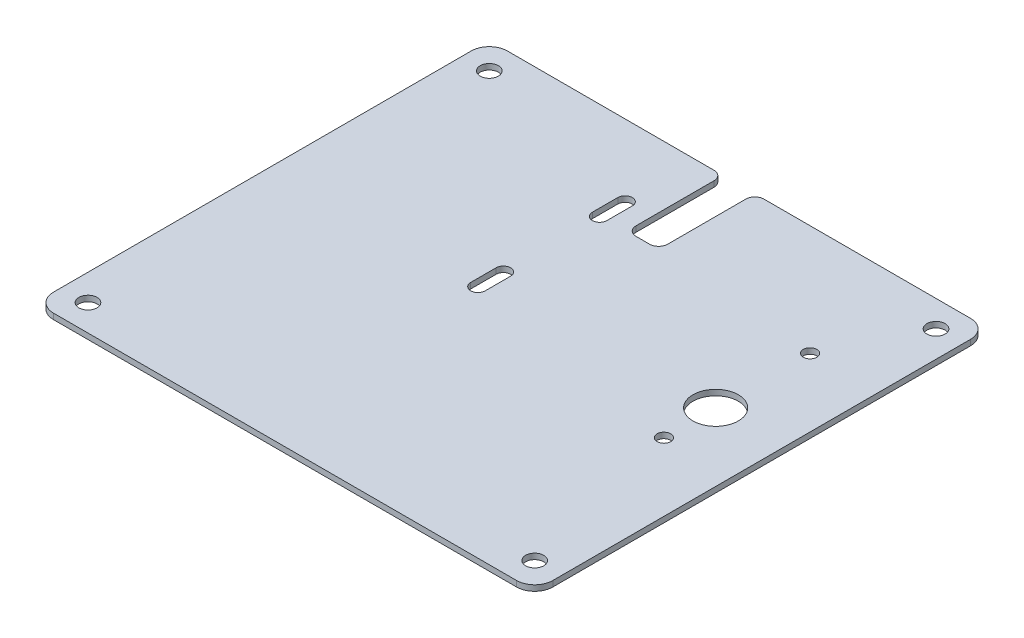
SolidWorks part; units mm, degrees
ref_plane "Front Plane" through (0, 0, 0) normal (0, 0, 1) x (1, 0, 0)
ref_plane "Top Plane" through (0, 0, 0) normal (0, 1, 0) x (1, 0, 0)
ref_plane "Right Plane" through (0, 0, 0) normal (1, 0, 0) x (0, 0, -1)
sketch "Sketch1" plane through (0, 0, 0) normal (0, 1, 0) x (1, 0, 0)
  line L0 (0, 50.038) -> (0, 69.85) construction
  line L1 (69.85, 63.5) -> (4.445, 63.5)
  line L2 (69.85, 63.5) -> (69.85, -63.5)
  line L3 (69.85, -63.5) -> (-69.85, -63.5)
  line L4 (-69.85, 63.5) -> (-69.85, -63.5)
  line L5 (69.85, 63.5) -> (-69.85, -63.5) construction
  line L6 (69.85, -63.5) -> (-69.85, 63.5) construction
  line L7 (-4.445, 63.5) -> (-69.85, 63.5)
  line L8 (4.445, 36.576) -> (-4.445, 36.576)
  line L9 (4.445, 36.576) -> (4.445, 63.5)
  line L11 (-4.445, 36.576) -> (-4.445, 63.5)
  line L12 (4.445, 36.576) -> (-4.445, 63.5) construction
  line L13 (4.445, 63.5) -> (-4.445, 36.576) construction
  line L14 (-11.811, 43.434) -> (-11.811, 36.322) construction
  line L15 (-9.779, 43.434) -> (-9.779, 36.322)
  line L16 (-13.843, 43.434) -> (-13.843, 36.322)
  line L17 (-11.811, 9.398) -> (-11.811, 2.286) construction
  line L18 (-9.779, 9.398) -> (-9.779, 2.286)
  line L19 (-13.843, 9.398) -> (-13.843, 2.286)
  line L20 (-11.811, 9.398) -> (-11.811, 43.434) construction
  line L21 (50.8, -8.304) -> (50.8, 32.59) construction
  circle A0 centre (-62.484, 56.134) radius 2.54
  circle A2 centre (-62.484, 56.134) radius 7.366 construction
  circle A3 centre (-62.484, -56.134) radius 2.54
  circle A4 centre (-62.484, -56.134) radius 7.366 construction
  circle A5 centre (62.484, 56.134) radius 2.54
  circle A6 centre (62.484, 56.134) radius 7.366 construction
  circle A7 centre (62.484, -56.134) radius 2.54
  circle A8 centre (62.484, -56.134) radius 7.366 construction
  arc A9 (-9.779, 43.434) -> (-13.843, 43.434) centre (-11.811, 43.434) ccw
  arc A10 (-13.843, 36.322) -> (-9.779, 36.322) centre (-11.811, 36.322) ccw
  arc A11 (-9.779, 9.398) -> (-13.843, 9.398) centre (-11.811, 9.398) ccw
  arc A12 (-13.843, 2.286) -> (-9.779, 2.286) centre (-11.811, 2.286) ccw
  circle A13 centre (50.8, -8.304) radius 1.905
  circle A14 centre (50.8, 32.59) radius 1.905
  circle A15 centre (50.8, 6.174) radius 6.35
  point P0 (0, 0)
  point P24 (-11.811, 39.878)
  point P31 (-11.811, 5.842)
  point P42 (0, 36.576)
  point P47 (45.8371, -14.654)
  point P48 (0, 69.85)
  dimension "D3" = 5.08
  dimension "D4" = 4.826
  dimension "D5" = 26.924
  dimension "D6" = 8.89
  dimension "D8" = 2.032
  dimension "D13" = 3.81
  dimension "D14" = 12.7
  dimension "D1" = 139.7
  dimension "D2" = 127
  dimension "D7" = 34.036
  dimension "D9" = 7.112
  dimension "D10" = 11.811
  dimension "D11" = 0.254
  dimension "D12" = 40.894
  dimension "D15" = 14.478
  dimension "D16" = 19.05
  dimension "D17" = 55.196
extrude "Boss-Extrude1" add sketch "Sketch1" against normal blind 1.5875
fillet "Fillet1" radius 5.08 4 edges at (-69.85, -0.7937, 63.5) (69.85, -0.7937, 63.5) (69.85, -0.7937, -63.5) (-69.85, -0.7937, -63.5)
fillet "Fillet2" radius 2.54 4 edges at (4.445, -0.7937, -36.576) (-4.445, -0.7937, -36.576) (4.445, -0.7937, -63.5) (-4.445, -0.7937, -63.5)
